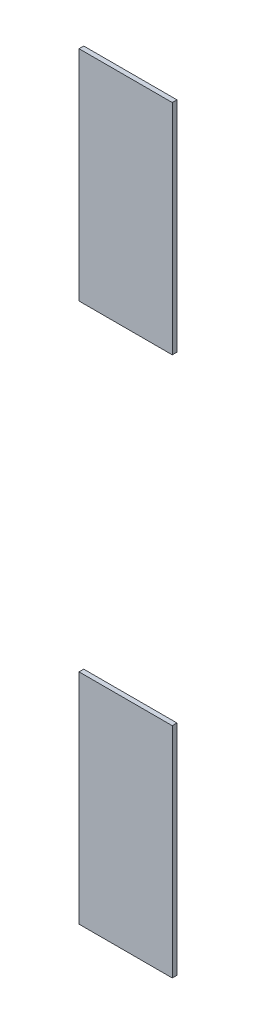
SolidWorks part; units mm, degrees
ref_plane "Спереди" through (0, 0, 0) normal (0, 0, 1) x (1, 0, 0)
ref_plane "Сверху" through (0, 0, 0) normal (0, 1, 0) x (1, 0, 0)
ref_plane "Справа" through (0, 0, 0) normal (1, 0, 0) x (0, 0, -1)
ref_plane "Плоскость1" through (0, 0, 0) normal (0, 0, -1) x (-1, 0, 0)
sketch "Эскиз1" plane through (0, 0, 0) normal (0, 0, -1) x (-1, 0, 0)
  line L0 (-32.55, 50.225) -> (-32.55, 43.25)
  line L1 (-32.55, 43.25) -> (-29.575, 43.25)
  line L2 (-29.575, 43.25) -> (-29.575, 50.225)
  line L3 (-29.575, 50.225) -> (-32.55, 50.225)
  line L5 (-31.0625, 38.125) -> (-30.067, 38.125) construction
  line L6 (-32.55, 33) -> (-29.575, 33)
  line L7 (-32.55, 50.225) -> (-29.575, 50.225)
  line L8 (-32.55, 50.225) -> (-32.55, 43.25)
  line L9 (-32.55, 43.25) -> (-29.575, 43.25)
  line L10 (-29.575, 50.225) -> (-29.575, 43.25)
  line L11 (-29.575, 26.025) -> (-29.575, 33)
  line L12 (-32.55, 26.025) -> (-29.575, 26.025)
  line L13 (-32.55, 26.025) -> (-32.55, 33)
extrude "Бобышка-Вытянуть1" add sketch "Эскиз1" against normal blind 0.15 contours L2 L3 L0 L1 | L13 L12 L11 L6
